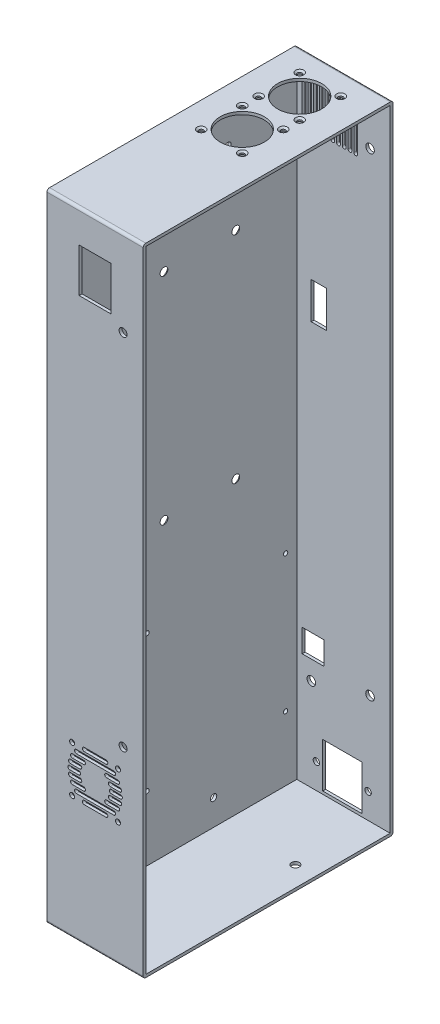
SolidWorks part; units mm, degrees
ref_plane "Front Plane" through (0, 0, 0) normal (0, 0, 1) x (1, 0, 0)
ref_plane "Top Plane" through (0, 0, 0) normal (0, 1, 0) x (1, 0, 0)
ref_plane "Right Plane" through (0, 0, 0) normal (1, 0, 0) x (0, 0, -1)
sketch "Sketch1" plane through (0, 0, 0) normal (1, 0, 0) x (0, 0, -1)
  line L0 (-87, 221.5) -> (87, -221.5) construction
  line L1 (-87, 221.5) -> (87, 221.5)
  line L2 (-87, 221.5) -> (-87, -221.5)
  line L3 (-87, -221.5) -> (87, -221.5)
  line L4 (87, 221.5) -> (87, -221.5)
  dimension "D1" = 443
  dimension "D2" = 174
extrude "Boss-Extrude1" add sketch "Sketch1" along normal blind 2
sketch "Sketch2" plane through (2, 0, 0) normal (1, 0, 0) x (0, 0, -1)
  line L8 (-85, 219.5) -> (-85, -219.5)
  line L9 (-85, -219.5) -> (85, -219.5)
  line L10 (85, -219.5) -> (85, 219.5)
  line L11 (85, 219.5) -> (-85, 219.5)
  line L12 (-85, 219.5) -> (-85, -219.5)
  line L13 (-85, -219.5) -> (85, -219.5)
  line L14 (85, -219.5) -> (85, 219.5)
  line L15 (85, 219.5) -> (-85, 219.5)
  line L16 (-87, 221.5) -> (-87, -221.5)
  line L17 (-87, -221.5) -> (87, -221.5)
  line L18 (87, -221.5) -> (87, 221.5)
  line L19 (87, 221.5) -> (-87, 221.5)
  line L20 (-87, 221.5) -> (-87, -221.5)
  line L21 (-87, -221.5) -> (87, -221.5)
  line L22 (87, -221.5) -> (87, 221.5)
  line L23 (87, 221.5) -> (-87, 221.5)
  dimension "D1" = 2
  dimension "D2" = 0
extrude "Boss-Extrude2" add sketch "Sketch2" along normal blind 65
fillet "Fillet1" radius 1.8 4 edges at (33.5, -221.5, -87) (33.5, -221.5, 87) (33.5, 221.5, -87) (33.5, 221.5, 87)
sketch "Sketch4" plane through (0, 0, 87) normal (0, 0, 1) x (1, 0, 0)
  line L0 (67, -221.5) -> (0, -221.5) construction
  line L1 (22.425, 199) -> (44.575, 199)
  line L2 (22.425, 199) -> (22.425, 168.5)
  line L3 (22.425, 168.5) -> (44.575, 168.5)
  line L4 (44.575, 199) -> (44.575, 168.5)
  line L6 (17.5, -103.5) -> (49.5, -135.5) construction
  line L7 (15.8, -119.5) -> (22.2, -119.5) construction
  line L8 (15.8, -118.2) -> (22.2, -118.2)
  line L9 (15.8, -120.8) -> (22.2, -120.8)
  line L10 (16.2579, -115.5) -> (22.9317, -115.5) construction
  line L11 (16.2579, -114.2) -> (22.9317, -114.2)
  line L12 (16.2579, -116.8) -> (22.9317, -116.8)
  line L13 (17.7111, -111.5) -> (25.5194, -111.5) construction
  line L14 (17.7111, -110.2) -> (25.5194, -110.2)
  line L15 (17.7111, -112.8) -> (25.5194, -112.8)
  line L16 (20.4889, -107.5) -> (46.5111, -107.5) construction
  line L17 (20.4889, -106.2) -> (46.5111, -106.2)
  line L18 (20.4889, -108.8) -> (46.5111, -108.8)
  line L19 (25.931, -103.5) -> (41.069, -103.5) construction
  line L20 (25.931, -102.2) -> (41.069, -102.2)
  line L21 (25.931, -104.8) -> (41.069, -104.8)
  line L22 (16.2579, -123.5) -> (22.9317, -123.5) construction
  line L23 (16.2579, -122.2) -> (22.9317, -122.2)
  line L24 (16.2579, -124.8) -> (22.9317, -124.8)
  line L25 (17.7111, -127.5) -> (25.5194, -127.5) construction
  line L26 (17.7111, -126.2) -> (25.5194, -126.2)
  line L27 (17.7111, -128.8) -> (25.5194, -128.8)
  line L28 (41.4806, -111.5) -> (49.2889, -111.5) construction
  line L29 (41.4806, -110.2) -> (49.2889, -110.2)
  line L30 (41.4806, -112.8) -> (49.2889, -112.8)
  line L31 (44.0683, -115.5) -> (50.7421, -115.5) construction
  line L32 (44.0683, -114.2) -> (50.7421, -114.2)
  line L33 (44.0683, -116.8) -> (50.7421, -116.8)
  line L34 (44.8, -119.5) -> (51.2, -119.5) construction
  line L35 (44.8, -118.2) -> (51.2, -118.2)
  line L36 (44.8, -120.8) -> (51.2, -120.8)
  line L37 (44.0683, -123.5) -> (50.7421, -123.5) construction
  line L38 (44.0683, -122.2) -> (50.7421, -122.2)
  line L39 (44.0683, -124.8) -> (50.7421, -124.8)
  line L40 (41.4806, -127.5) -> (49.2889, -127.5) construction
  line L41 (41.4806, -126.2) -> (49.2889, -126.2)
  line L42 (41.4806, -128.8) -> (49.2889, -128.8)
  line L43 (20.4889, -131.5) -> (46.5111, -131.5) construction
  line L44 (20.4889, -130.2) -> (46.5111, -130.2)
  line L45 (20.4889, -132.8) -> (46.5111, -132.8)
  line L46 (25.931, -135.5) -> (41.069, -135.5) construction
  line L47 (25.931, -134.2) -> (41.069, -134.2)
  line L48 (25.931, -136.8) -> (41.069, -136.8)
  line L49 (33.5, 199) -> (33.5, 221.5) construction
  line L50 (0, 221.5) -> (67, 221.5) construction
  circle A0 centre (17.5, -135.5) radius 1.75
  circle A1 centre (49.5, -135.5) radius 1.75
  circle A2 centre (17.5, -103.5) radius 1.75
  circle A3 centre (49.5, -103.5) radius 1.75
  circle A4 centre (33.5, -119.5) radius 10 construction
  circle A5 centre (33.5, -119.5) radius 19 construction
  arc A6 (15.8, -118.2) -> (15.8, -120.8) centre (15.8, -119.5) ccw
  arc A7 (22.2, -120.8) -> (22.2, -118.2) centre (22.2, -119.5) ccw
  arc A8 (16.2579, -114.2) -> (16.2579, -116.8) centre (16.2579, -115.5) ccw
  arc A9 (22.9317, -116.8) -> (22.9317, -114.2) centre (22.9317, -115.5) ccw
  arc A10 (17.7111, -110.2) -> (17.7111, -112.8) centre (17.7111, -111.5) ccw
  arc A11 (25.5194, -112.8) -> (25.5194, -110.2) centre (25.5194, -111.5) ccw
  arc A12 (20.4889, -106.2) -> (20.4889, -108.8) centre (20.4889, -107.5) ccw
  arc A13 (46.5111, -108.8) -> (46.5111, -106.2) centre (46.5111, -107.5) ccw
  arc A14 (25.931, -102.2) -> (25.931, -104.8) centre (25.931, -103.5) ccw
  arc A15 (41.069, -104.8) -> (41.069, -102.2) centre (41.069, -103.5) ccw
  arc A16 (16.2579, -122.2) -> (16.2579, -124.8) centre (16.2579, -123.5) ccw
  arc A17 (22.9317, -124.8) -> (22.9317, -122.2) centre (22.9317, -123.5) ccw
  arc A18 (17.7111, -126.2) -> (17.7111, -128.8) centre (17.7111, -127.5) ccw
  arc A19 (25.5194, -128.8) -> (25.5194, -126.2) centre (25.5194, -127.5) ccw
  arc A20 (41.4806, -110.2) -> (41.4806, -112.8) centre (41.4806, -111.5) ccw
  arc A21 (49.2889, -112.8) -> (49.2889, -110.2) centre (49.2889, -111.5) ccw
  arc A22 (44.0683, -114.2) -> (44.0683, -116.8) centre (44.0683, -115.5) ccw
  arc A23 (50.7421, -116.8) -> (50.7421, -114.2) centre (50.7421, -115.5) ccw
  arc A24 (44.8, -118.2) -> (44.8, -120.8) centre (44.8, -119.5) ccw
  arc A25 (51.2, -120.8) -> (51.2, -118.2) centre (51.2, -119.5) ccw
  arc A26 (44.0683, -122.2) -> (44.0683, -124.8) centre (44.0683, -123.5) ccw
  arc A27 (50.7421, -124.8) -> (50.7421, -122.2) centre (50.7421, -123.5) ccw
  arc A28 (41.4806, -126.2) -> (41.4806, -128.8) centre (41.4806, -127.5) ccw
  arc A29 (49.2889, -128.8) -> (49.2889, -126.2) centre (49.2889, -127.5) ccw
  arc A30 (20.4889, -130.2) -> (20.4889, -132.8) centre (20.4889, -131.5) ccw
  arc A31 (46.5111, -132.8) -> (46.5111, -130.2) centre (46.5111, -131.5) ccw
  arc A32 (25.931, -134.2) -> (25.931, -136.8) centre (25.931, -135.5) ccw
  arc A33 (41.069, -136.8) -> (41.069, -134.2) centre (41.069, -135.5) ccw
  circle A34 centre (53, -88.5) radius 2.75
  circle A35 centre (53, 161.5) radius 2.75
  point P25 (19, -119.5)
  point P32 (19.5948, -115.5)
  point P39 (21.6152, -111.5)
  point P46 (33.5, -107.5)
  point P53 (33.5, -103.5)
  point P60 (19.5948, -123.5)
  point P65 (21.6152, -127.5)
  point P72 (45.3848, -111.5)
  point P79 (47.4052, -115.5)
  point P86 (48, -119.5)
  point P93 (47.4052, -123.5)
  point P100 (45.3848, -127.5)
  point P107 (33.5, -131.5)
  point P114 (33.5, -135.5)
  dimension "D5" = 3.5
  dimension "D6" = 38
  dimension "D7" = 20
  dimension "D4" = 5.5
  dimension "D1" = 30.5
  dimension "D2" = 22.15
  dimension "D3" = 390
  dimension "D8" = 2.6
  dimension "D9" = 4
  dimension "D10" = 4
  dimension "D11" = 4
  dimension "D12" = 4
  dimension "D13" = 4
  dimension "D14" = 4
  dimension "D15" = 4
  dimension "D16" = 4
extrude "Cut-Extrude1" cut sketch "Sketch4" against normal blind 5
sketch "Sketch5" plane through (0, 0, -87) normal (0, 0, -1) x (-1, 0, 0)
  line L0 (-47.3, -186.4) -> (-20, -217.5) construction
  line L1 (-47.3, -186.4) -> (-20, -186.4)
  line L2 (-47.3, -186.4) -> (-47.3, -217.5)
  line L3 (-47.3, -217.5) -> (-20, -217.5)
  line L4 (-20, -186.4) -> (-20, -217.5)
  line L5 (-51.65, -201.95) -> (-33.65, -201.95) construction
  line L6 (-33.65, -201.95) -> (-15.65, -201.95) construction
  line L7 (0, -221.5) -> (-67, -221.5) construction
  line L8 (0, -219.7) -> (0, 219.7) construction
  line L9 (-7.778, -139.89) -> (-7.778, -127.89) construction
  line L10 (-21.081, -125.89) -> (-5.778, -125.89)
  line L11 (-21.081, -125.89) -> (-21.081, -141.89)
  line L12 (-21.081, -141.89) -> (-5.778, -141.89)
  line L13 (-5.778, -125.89) -> (-5.778, -141.89)
  line L14 (-19.081, -139.89) -> (-7.778, -139.89) construction
  line L15 (-19.081, -139.89) -> (-19.081, -127.89) construction
  line L16 (-19.081, -127.89) -> (-7.778, -127.89) construction
  line L17 (-43, 213.5) -> (-43, 178.5) construction
  line L18 (-22.5, 87) -> (-12, 87)
  line L19 (-22.5, 87) -> (-22.5, 61.5)
  line L20 (-22.5, 61.5) -> (-12, 61.5)
  line L21 (-12, 87) -> (-12, 61.5)
  line L22 (-13, 71) -> (-13, 86) construction
  line L23 (-13, 86) -> (-21, 86) construction
  line L24 (-41.7, 213.5) -> (-41.7, 178.5)
  line L25 (-44.3, 213.5) -> (-44.3, 178.5)
  line L26 (-35, 213.5) -> (-35, 178.5) construction
  line L27 (-21.5, 62.5) -> (-13.5, 62.5) construction
  line L28 (-33.7, 213.5) -> (-33.7, 178.5)
  line L29 (-21.5, 77.5) -> (-21.5, 62.5) construction
  line L30 (-39, 213.5) -> (-39, 178.5) construction
  line L31 (-37.7, 213.5) -> (-37.7, 178.5)
  line L32 (-40.3, 213.5) -> (-40.3, 178.5)
  line L33 (-67, 221.5) -> (0, 221.5) construction
  line L34 (-67, -219.7) -> (-67, 219.7) construction
  line L35 (-36.3, 213.5) -> (-36.3, 178.5)
  line L36 (-31, 213.5) -> (-31, 178.5) construction
  line L37 (-29.7, 213.5) -> (-29.7, 178.5)
  line L38 (-32.3, 213.5) -> (-32.3, 178.5)
  line L39 (-27, 213.5) -> (-27, 178.5) construction
  line L40 (-25.7, 213.5) -> (-25.7, 178.5)
  line L41 (-28.3, 213.5) -> (-28.3, 178.5)
  line L42 (-23, 213.5) -> (-23, 178.5) construction
  line L43 (-21.7, 213.5) -> (-21.7, 178.5)
  line L44 (-24.3, 213.5) -> (-24.3, 178.5)
  line L48 (-15, 213.5) -> (-15, 178.5) construction
  line L49 (-13.7, 213.5) -> (-13.7, 178.5)
  line L50 (-16.3, 213.5) -> (-16.3, 178.5)
  line L51 (-7, 213.5) -> (-7, 178.5) construction
  line L52 (-5.7, 213.5) -> (-5.7, 178.5)
  line L53 (-8.3, 213.5) -> (-8.3, 178.5)
  line L54 (-43, 213.5) -> (-39, 213.5) construction
  line L55 (-39, 213.5) -> (-35, 213.5) construction
  line L56 (-35, 213.5) -> (-31, 213.5) construction
  line L57 (-31, 213.5) -> (-27, 213.5) construction
  line L58 (-27, 213.5) -> (-23, 213.5) construction
  line L59 (-23, 213.5) -> (-19, 213.5) construction
  line L60 (-19, 213.5) -> (-15, 213.5) construction
  line L61 (-15, 213.5) -> (-11, 213.5) construction
  line L62 (-19, 213.5) -> (-19, 178.5) construction
  line L63 (-17.7, 213.5) -> (-17.7, 178.5)
  line L64 (-20.3, 213.5) -> (-20.3, 178.5)
  line L65 (-11, 213.5) -> (-11, 178.5) construction
  line L66 (-9.7, 213.5) -> (-9.7, 178.5)
  line L67 (-12.3, 213.5) -> (-12.3, 178.5)
  line L74 (-11, 213.5) -> (-15, 213.5) construction
  line L75 (-11, 213.5) -> (-7, 213.5) construction
  circle A0 centre (-51.65, -201.95) radius 2.25
  circle A1 centre (-15.65, -201.95) radius 2.25
  circle A2 centre (-12.096, -155.07) radius 3
  arc A3 (-41.7, 213.5) -> (-44.3, 213.5) centre (-43, 213.5) ccw
  arc A4 (-44.3, 178.5) -> (-41.7, 178.5) centre (-43, 178.5) ccw
  arc A5 (-37.7, 213.5) -> (-40.3, 213.5) centre (-39, 213.5) ccw
  arc A6 (-40.3, 178.5) -> (-37.7, 178.5) centre (-39, 178.5) ccw
  arc A7 (-33.7, 213.5) -> (-36.3, 213.5) centre (-35, 213.5) ccw
  arc A8 (-36.3, 178.5) -> (-33.7, 178.5) centre (-35, 178.5) ccw
  arc A9 (-29.7, 213.5) -> (-32.3, 213.5) centre (-31, 213.5) ccw
  arc A10 (-32.3, 178.5) -> (-29.7, 178.5) centre (-31, 178.5) ccw
  arc A11 (-25.7, 213.5) -> (-28.3, 213.5) centre (-27, 213.5) ccw
  arc A12 (-28.3, 178.5) -> (-25.7, 178.5) centre (-27, 178.5) ccw
  arc A13 (-21.7, 213.5) -> (-24.3, 213.5) centre (-23, 213.5) ccw
  arc A14 (-24.3, 178.5) -> (-21.7, 178.5) centre (-23, 178.5) ccw
  circle A15 centre (-53, 186.5) radius 3
  circle A16 centre (-53, -143.5) radius 3
  arc A17 (-13.7, 213.5) -> (-16.3, 213.5) centre (-15, 213.5) ccw
  arc A18 (-16.3, 178.5) -> (-13.7, 178.5) centre (-15, 178.5) ccw
  arc A19 (-5.7, 213.5) -> (-8.3, 213.5) centre (-7, 213.5) ccw
  arc A20 (-8.3, 178.5) -> (-5.7, 178.5) centre (-7, 178.5) ccw
  arc A21 (-17.7, 213.5) -> (-20.3, 213.5) centre (-19, 213.5) ccw
  arc A22 (-20.3, 178.5) -> (-17.7, 178.5) centre (-19, 178.5) ccw
  arc A23 (-9.7, 213.5) -> (-12.3, 213.5) centre (-11, 213.5) ccw
  arc A24 (-12.3, 178.5) -> (-9.7, 178.5) centre (-11, 178.5) ccw
  point P42 (-43, 196)
  point P47 (-39, 196)
  point P60 (-35, 196)
  point P65 (-31, 196)
  point P72 (-27, 196)
  point P79 (-23, 196)
  point P93 (-15, 196)
  point P100 (-7, 196)
  point P118 (-19, 196)
  point P123 (-11, 196)
  dimension "D4" = 4.5
  dimension "D7" = 6
  dimension "D16" = 8
  dimension "D19" = 2.6
  dimension "D20" = 4
  dimension "D21" = 6
  dimension "D1" = 27.3
  dimension "D2" = 31.1
  dimension "D3" = 36
  dimension "D5" = 4
  dimension "D6" = 20
  dimension "D8" = 2
  dimension "D9" = 2
  dimension "D10" = 2
  dimension "D11" = 2
  dimension "D12" = 1
  dimension "D13" = 1
  dimension "D14" = 1
  dimension "D15" = 1
  dimension "D17" = 35
  dimension "D18" = 24
extrude "Cut-Extrude2" cut sketch "Sketch5" against normal blind 5
sketch "Sketch11" plane through (2, 0, 0) normal (1, 0, 0) x (0, 0, -1)
  line L0 (-85.2, -221.5) -> (85.2, -221.5) construction
  line L1 (85.2, 221.5) -> (-85.2, 221.5) construction
  line L2 (87, -219.7) -> (87, 219.7) construction
  circle A0 centre (-19.33, -79.31) radius 1.5
  circle A1 centre (77.19, -79.31) radius 1.5
  circle A2 centre (-19.33, -174.56) radius 1.5
  circle A3 centre (77.19, -174.56) radius 1.5
  circle A4 centre (-7.5, 133) radius 1.5
  circle A5 centre (42.5, 133) radius 1.5
  circle A6 centre (42.5, -17) radius 1.5
  circle A7 centre (-7.5, -17) radius 1.5
  circle A8 centre (27, -201.5) radius 2.25
  circle A9 centre (37, 186.5) radius 2.25
  dimension "D1" = 3
  dimension "D2" = 3
  dimension "D4" = 4.5
  dimension "D8" = 4.5
  dimension "D3" = 20
  dimension "D5" = 60
  dimension "D6" = 35
  dimension "D7" = 50
extrude "Cut-Extrude4" cut sketch "Sketch11" against normal blind 5
hole_wizard "CSK for M4 Flat Head Machine Screw1" positions "Sketch13" profile "Sketch12" countersink size "M4" standard "Ansi Metric"
sketch "Sketch13" plane through (0, 0, 0) normal (-1, 0, 0) x (0, 0, 1)
  point P0 (-42.5, 133)
  point P1 (7.5, 133)
  point P4 (7.5, -17)
  point P7 (-42.5, -17)
sketch "Sketch12" plane through (0, 133, -42.5) normal (0, 1, 0) x (0, 0, 1)
  line L0 (0, 0) -> (0, 11.3519)
  line L1 (0, 11.3519) -> (2.25, 10)
  line L2 (2.25, 10) -> (2.25, 2.45)
  line L3 (2.25, 2.45) -> (4.7, 0)
  line L5 (4.7, 0) -> (0, 0)
  line L6 (-2.25, 2.45) -> (-4.7, 0) construction
  line L10 (0, 11.3519) -> (-2.25, 10) construction
  line L11 (0, -6.35) -> (0, 107.95) construction
  dimension "Hole Dia." = 4.5
  dimension "Hole Depth" = 10
  dimension "Near C'Sink Dia." = 9.4
  dimension "Near C'Sink Angle" = 90
  dimension "Drill Angle" = 118
sketch "Sketch14" plane through (0, 221.5, 0) normal (0, 1, 0) x (1, 0, 0)
  line L0 (0, 87) -> (67, 87) construction
  line L1 (0, 85.2) -> (0, -85.2) construction
  line L2 (46.29, 71.29) -> (17.71, 42.71) construction
  line L3 (17.71, 31.29) -> (46.29, 2.71) construction
  circle A0 centre (32, 57) radius 15.365
  circle A1 centre (17.71, 71.29) radius 1.5
  circle A2 centre (46.29, 71.29) radius 1.5
  circle A3 centre (46.29, 42.71) radius 1.5
  circle A4 centre (17.71, 42.71) radius 1.5
  circle A5 centre (32, 17) radius 15.365
  circle A6 centre (17.71, 31.29) radius 1.5
  circle A7 centre (46.29, 31.29) radius 1.5
  circle A8 centre (46.29, 2.71) radius 1.5
  circle A9 centre (17.71, 2.71) radius 1.5
  dimension "D5" = 30.73
  dimension "D6" = 3
  dimension "D8" = 40
  dimension "D1" = 30
  dimension "D2" = 32
  dimension "D3" = 28.58
  dimension "D4" = 28.58
  dimension "D7" = 28.58
extrude "Cut-Extrude5" cut sketch "Sketch14" against normal blind 10
hole_wizard "CSK for #4 Flat Head Machine Screw (100)1" positions "Sketch16" profile "Sketch15" countersink size "#4" standard "Ansi Inch"
sketch "Sketch16" plane through (0, 221.5, 0) normal (0, 1, 0) x (-1, 0, 0)
  point P0 (-17.71, -71.29)
  point P1 (-17.71, -42.71)
  point P4 (-46.29, -42.71)
  point P7 (-46.29, -71.29)
  point P13 (-17.71, -31.29)
  point P16 (-46.29, -31.29)
  point P19 (-46.29, -2.71)
  point P22 (-17.71, -2.71)
sketch "Sketch15" plane through (17.71, 221.5, -71.29) normal (1, 0, 0) x (0, 0, 1)
  line L0 (0, 0) -> (0, 10.9806)
  line L1 (0, 10.9806) -> (1.6319, 10)
  line L2 (1.6319, 10) -> (1.6319, 1.0284)
  line L3 (1.6319, 1.0284) -> (2.8575, 0)
  line L5 (2.8575, 0) -> (0, 0)
  line L6 (-1.6319, 1.0284) -> (-2.8575, 0) construction
  line L10 (0, 10.9806) -> (-1.6319, 10) construction
  line L11 (0, -6.35) -> (0, 107.95) construction
  dimension "Hole Dia." = 3.2639
  dimension "Hole Depth" = 10
  dimension "Near C'Sink Dia." = 5.715
  dimension "Near C'Sink Angle" = 100
  dimension "Drill Angle" = 118
sketch "Sketch17" plane through (0, -221.5, 0) normal (0, -1, 0) x (1, 0, 0)
  circle A0 centre (53, -33) radius 2.75
  dimension "D1" = 5.5
extrude "Cut-Extrude6" cut sketch "Sketch17" against normal blind 10
